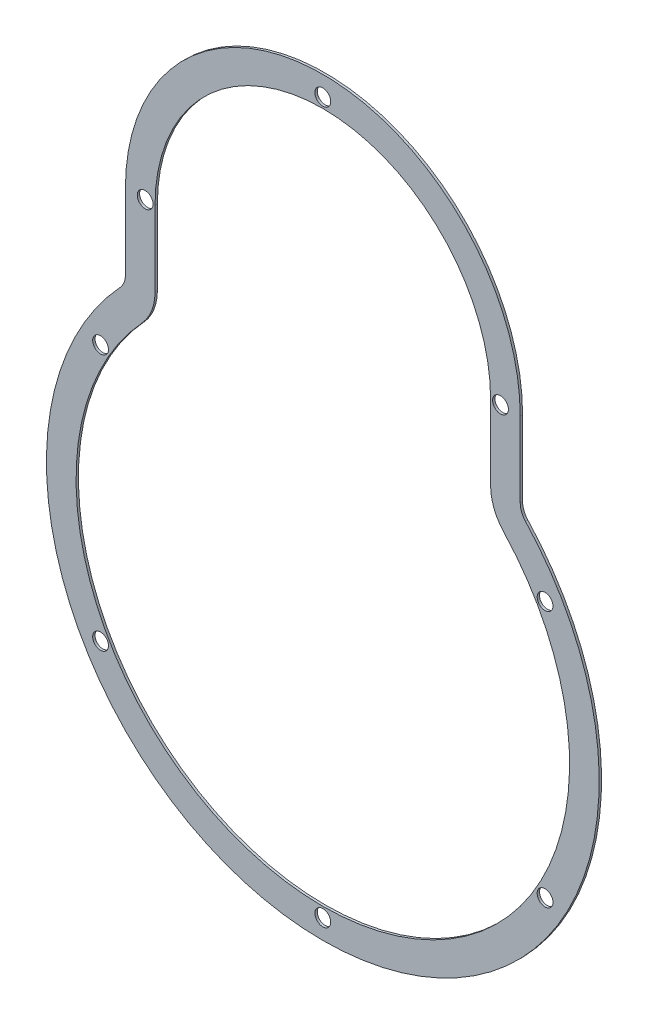
SolidWorks part; units mm, degrees
ref_plane "Front Plane" through (0, 0, 0) normal (0, 0, 1) x (1, 0, 0)
ref_plane "Top Plane" through (0, 0, 0) normal (0, 1, 0) x (1, 0, 0)
ref_plane "Right Plane" through (0, 0, 0) normal (1, 0, 0) x (0, 0, -1)
sketch "Sketch1" plane through (0, 0, 0) normal (0, 0, 1) x (1, 0, 0)
  line L0 (-53.975, 88.9) -> (-53.975, 64.7575)
  line L1 (53.975, 64.7575) -> (53.975, 88.9)
  line L4 (-63.5, 88.9) -> (-63.5, 64.7575)
  line L5 (63.5, 64.7575) -> (63.5, 88.9)
  arc A0 (53.975, 88.9) -> (-53.975, 88.9) centre (0, 88.9) ccw
  arc A1 (-58.2083, 53.9646) -> (-53.975, 64.7575) centre (-69.85, 64.7575) ccw
  arc A2 (-58.2083, 53.9646) -> (58.2083, 53.9646) centre (0, 0) ccw
  arc A3 (53.975, 64.7575) -> (58.2083, 53.9646) centre (69.85, 64.7575) ccw
  arc A8 (63.5, 88.9) -> (-63.5, 88.9) centre (0, 88.9) ccw
  arc A9 (-65.1933, 60.4404) -> (-63.5, 64.7575) centre (-69.85, 64.7575) ccw
  arc A10 (-65.1933, 60.4404) -> (65.1933, 60.4404) centre (0, 0) ccw
  arc A11 (63.5, 64.7575) -> (65.1933, 60.4404) centre (69.85, 64.7575) ccw
  circle A20 centre (-71.4904, -41.275) radius 2.54
  circle A21 centre (-71.4904, 41.275) radius 2.54
  circle A22 centre (-57.15, 88.9) radius 2.54
  circle A23 centre (0, 146.05) radius 2.54
  circle A24 centre (57.15, 88.9) radius 2.54
  circle A25 centre (71.4904, 41.275) radius 2.54
  circle A26 centre (71.4904, -41.275) radius 2.54
  circle A27 centre (0, -82.55) radius 2.54
  dimension "D2" = 9.525
extrude "Boss-Extrude2" add sketch "Sketch1" along normal blind 0.762
